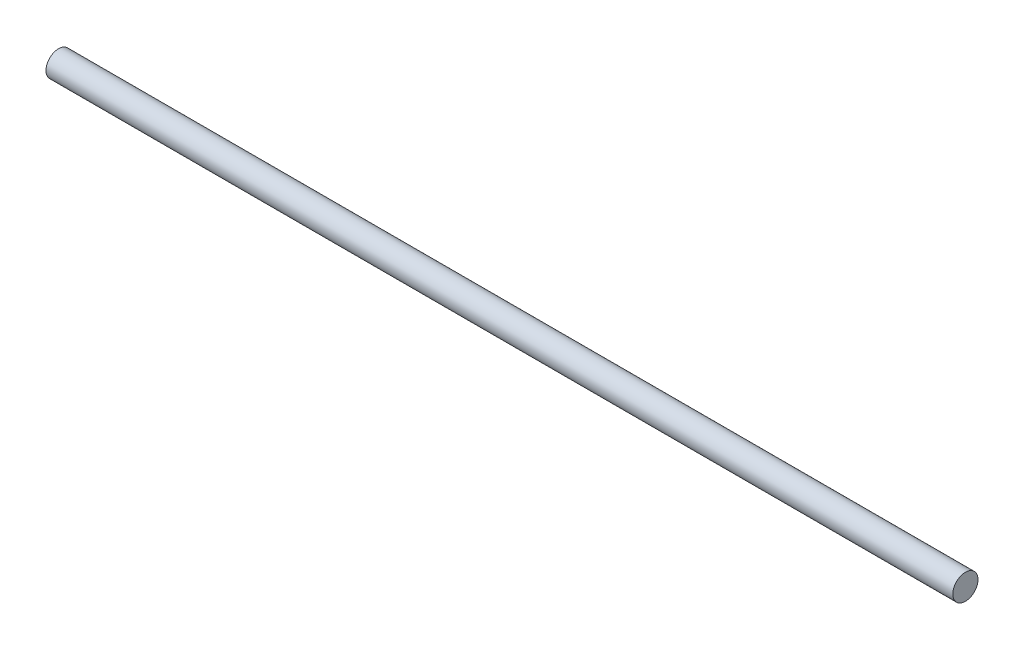
SolidWorks part; units mm, degrees
ref_plane "Front Plane" through (0, 0, 0) normal (0, 0, 1) x (1, 0, 0)
ref_plane "Top Plane" through (0, 0, 0) normal (0, 1, 0) x (1, 0, 0)
ref_plane "Right Plane" through (0, 0, 0) normal (1, 0, 0) x (0, 0, -1)
sketch "Sketch1" plane through (0, 0, 0) normal (0, 1, 0) x (1, 0, 0)
  line L0 (0, 0) -> (-18.8153, 0) construction
  line L1 (0, 0) -> (900, 0)
  line L2 (0, 0) -> (0, 12.5)
  line L3 (0, 12.5) -> (900, 12.5)
  line L4 (900, 0) -> (900, 12.5)
  dimension "D1" = 25
  dimension "900" = 900
revolve "Revolve1" add sketch "Sketch1" angle 360 about L0
